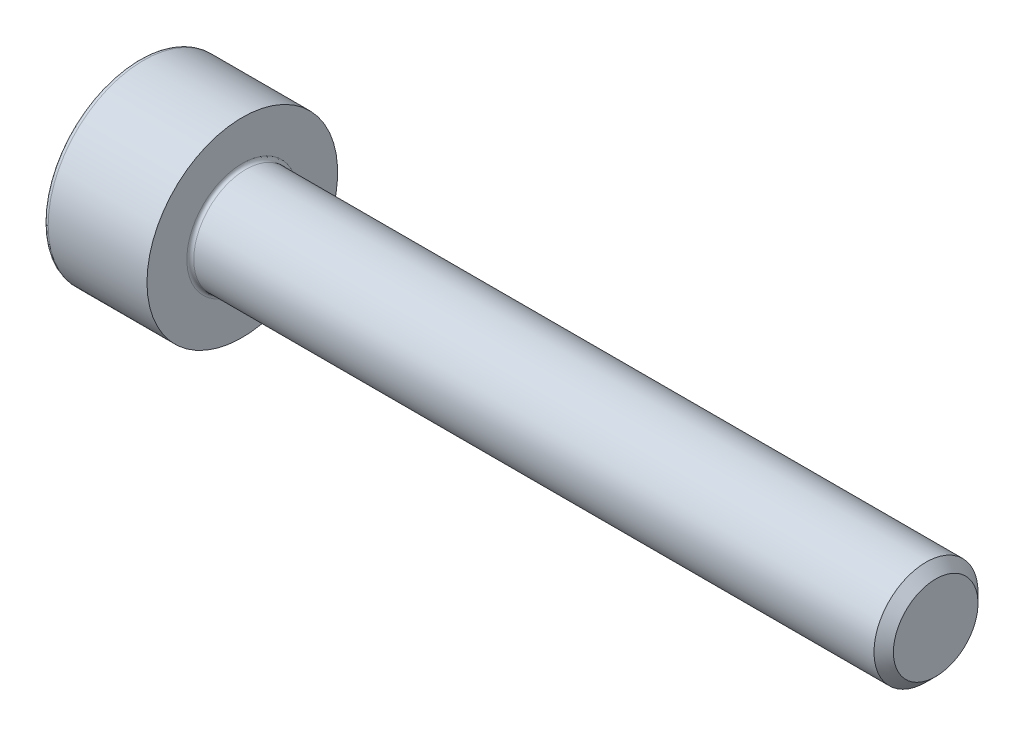
SolidWorks part; units mm, degrees
revolve "Base-Revolve" add sketch "BodySke"
sketch "BodySke" plane through (0, 0, 0) normal (0, 0, 1) x (1, 0, 0)
  line L0 (0, 0) -> (0, 2.75)
  line L1 (0, 2.75) -> (3, 2.75)
  line L2 (3, 2.75) -> (3, 1.5)
  line L3 (3, 1.5) -> (22.7195, 1.5)
  line L4 (23, 1.2195) -> (23, 0)
  line L5 (23, 0) -> (0, 0)
  line L6 (-31.75, 0) -> (127, 0) construction
  line L8 (23, 1.2195) -> (22.7195, 1.5)
  line L10 (23, -1.2195) -> (22.7195, -1.5) construction
  line L11 (3.5, 9.525) -> (3.5, 3.175) construction
  line L12 (3, 9.525) -> (3, 3.175) construction
  line L13 (-37, 9.525) -> (-37, 3.175) construction
  dimension "Body_ch_ang" = 45
  dimension "Advance" = 0.5
  dimension "Thread_length" = 60
cosmetic thread "ThreadCosmetic" [suppressed]
fillet "Fillet1" radius 0.1 1 edges at (3, 0, 1.5)
fillet "Fillet2" radius 0.15 1 edges at (0, 0, 2.75)
material "AISI Aço-ferramenta tipo A2"
ref_plane "Plane1" through (0, 0, 0) normal (0, 0, 1) x (1, 0, 0)
ref_plane "Plane2" through (0, 0, 0) normal (0, 1, 0) x (1, 0, 0)
ref_plane "Plane3" through (0, 0, 0) normal (1, 0, 0) x (0, 0, -1)
sketch "Sketch2" plane through (0, 0, 0) normal (0, 0, 1) x (1, 0, 0)
  line L0 (0, 1.28) -> (1.3, 1.28)
  line L1 (1.3, 1.28) -> (2.039, 0)
  line L2 (-31.75, 0) -> (127, 0) construction
  line L3 (2.039, 0) -> (0, 0)
  line L4 (0, 0) -> (0, 1.28)
  line L6 (0, 0) -> (47.625, 0) construction
  dimension "D2" = 60
revolve "Hex-PreBroach" cut sketch "Sketch2" angle 360 about L6
sketch "Sketch3" plane through (0, 0, 0) normal (-1, 0, 0) x (0, 0.5, 0.866)
  line L0 (0.739, 1.28) -> (-0.739, 1.28)
  line L1 (-0.739, 1.28) -> (-1.478, 0)
  line L2 (0.739, 1.28) -> (1.478, 0)
  line L3 (0.739, -1.28) -> (1.478, 0)
  line L4 (0.739, -1.28) -> (-0.739, -1.28)
  line L5 (-0.739, -1.28) -> (-1.478, 0)
extrude "Hex" cut sketch "Sketch3" against normal blind 1.3
sketch "ThdSchSke" plane through (0, 0, 0) normal (0, 0, 1) x (1, 0, 0)
  line L0 (4.5, -1.2195) -> (4.3036, -1.5)
  line L1 (4.5, -1.2195) -> (4.6964, -1.5)
  line L2 (4.6964, -1.5) -> (4.6964, -1.875)
  line L3 (-3.175, 0) -> (5.1513, 0) construction
  line L4 (0, 2.6) -> (0, -2.6) construction
  line L5 (4.6964, -1.875) -> (4.3036, -1.875)
  line L6 (4.3036, -1.875) -> (4.3036, -1.5)
revolve "ThreadSchematic" [suppressed] cut sketch "ThdSchSke" angle 360 about L3
pattern_linear "ThdSchPat" [suppressed]
equation "\"D2@Sketch3\" = \"Hex_size@Sketch3\" / 2"
equation "\"D1@Sketch3\" = \"Hex_size@Sketch3\" / 2"
equation "\"D1@Sketch2\" = \"Hex_size@Sketch3\" / 2"
equation "\"Thread_minor@ThreadCosmetic\"  =  \"Minor_dia@BodySke\""
equation "\"Depth@Sketch2\" =  \"Key_eng@Hex\""
equation "\"Thread_length@ThreadCosmetic\" = ((sgn( (\"Length@BodySke\" - \"Advance@BodySke\" * 3.0) - \"Thread_nom@BodySke\" )-1)*( (\"Length@BodySke\" - \"Advance@BodySke\" * 3.0) - \"Thread_nom@BodySke\" ))/-2+ \"Thread_nom@BodySke\""
equation "\"Thread_minor@ThdSchSke\" = \"Minor_dia@BodySke\""
equation "\"Diameter@ThdSchSke\" = \"Diameter@BodySke\""
equation "\"Overcut@ThdSchSke\" = \"Diameter@BodySke\" * 1.25"
equation "\"Start@ThdSchSke\" = \"Head_ht@BodySke\" + \"Length@BodySke\" - \"Thread_length@ThreadCosmetic\"  '---Non-countersunk---"
equation "\"Num_threads@ThdSchPat\" = int( \"Thread_length@ThreadCosmetic\" / \"Advance@BodySke\" + 0.999 )  + 1"
equation "\"Advance@ThdSchPat\" = \"Thread_length@ThreadCosmetic\" /  (\"Num_threads@ThdSchPat\" - 1) 'relax it"
equation "\"Num_threads@ThdSchPat\" = \"Num_threads@ThdSchPat\" - sgn( \"Num_threads@ThdSchPat\" - 1) '---chamfered tips only---"
